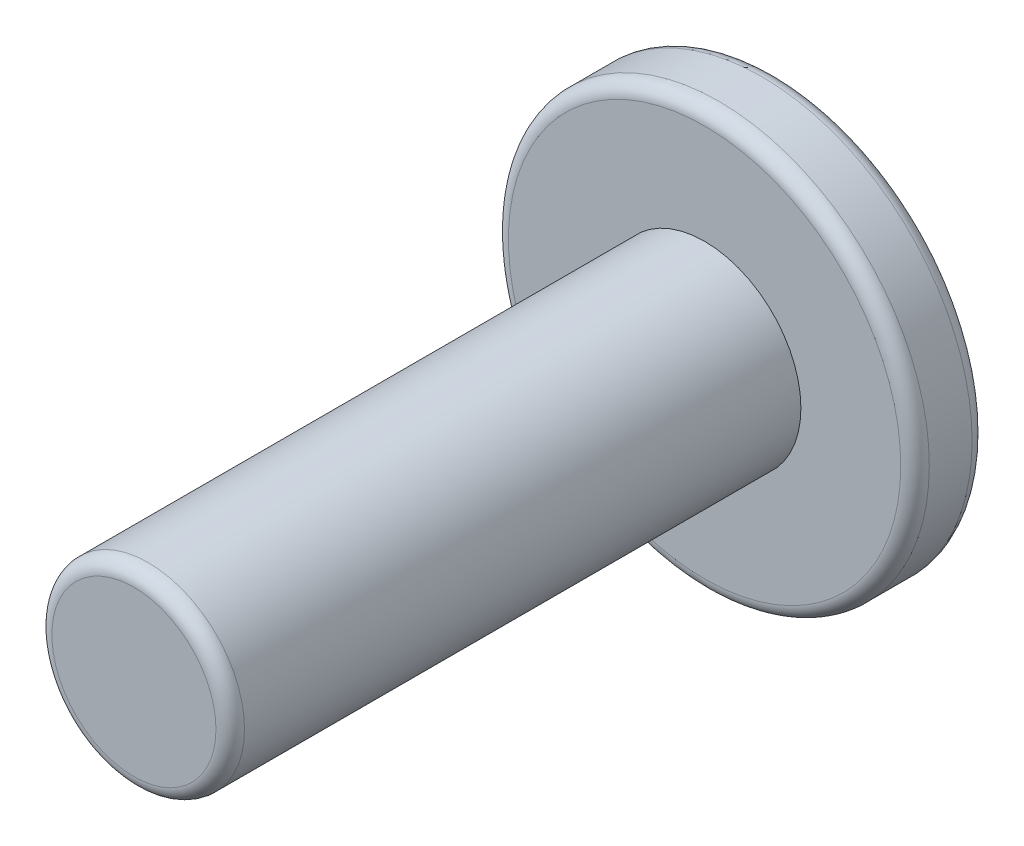
SolidWorks part; units mm, degrees
ref_plane "Front Plane" through (0, 0, 0) normal (0, 0, 1) x (1, 0, 0)
ref_plane "Top Plane" through (0, 0, 0) normal (0, 1, 0) x (1, 0, 0)
ref_plane "Right Plane" through (0, 0, 0) normal (1, 0, 0) x (0, 0, -1)
sketch "Sketch1" plane through (0, 0, 0) normal (0, 0, 1) x (1, 0, 0)
  circle A0 centre (0, 0) radius 2.95
  dimension "D1" = 5.9
extrude "Boss-Extrude1" add sketch "Sketch1" along normal blind 1
sketch "Sketch2" plane through (0, 0, 1) normal (0, 0, 1) x (1, 0, 0)
  circle A0 centre (0, 0) radius 1.35
  dimension "D1" = 2.7
extrude "Boss-Extrude2" add sketch "Sketch2" along normal blind 8
fillet "Fillet1" radius 0.2 3 edges at (1.35, 0, 9) (2.95, 0, 0) (2.95, 0, 1)
